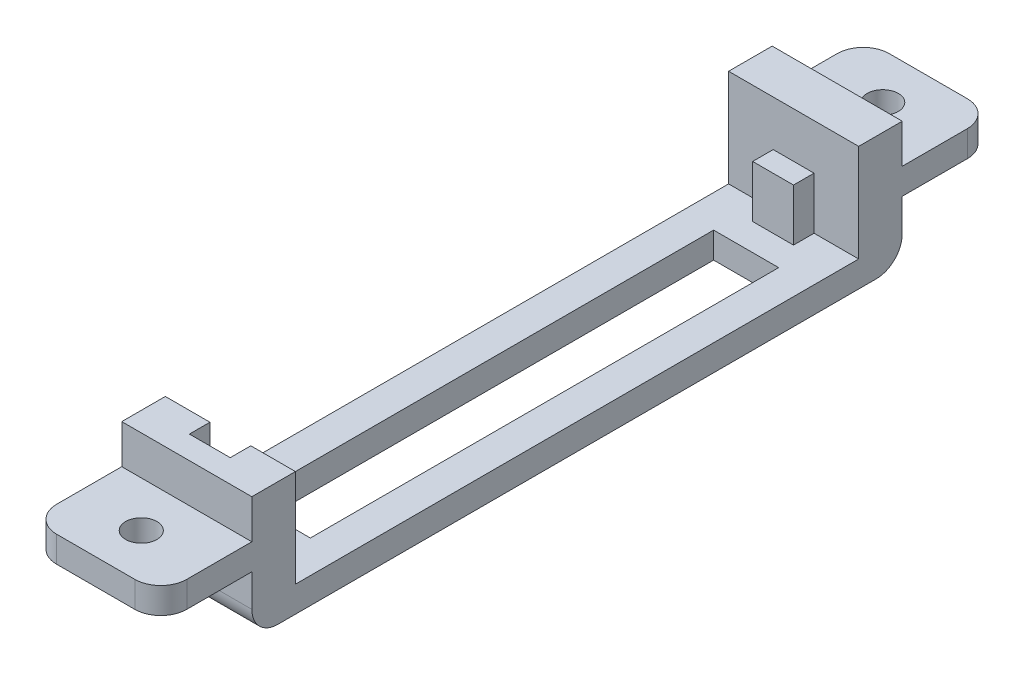
SolidWorks part; units mm, degrees
ref_plane "Front" through (0, 0, 0) normal (0, 0, 1) x (1, 0, 0)
ref_plane "Top" through (0, 0, 0) normal (0, 1, 0) x (1, 0, 0)
ref_plane "Right" through (0, 0, 0) normal (1, 0, 0) x (0, 0, -1)
sketch "Sketch1" plane through (0, 0, 0) normal (0, 1, 0) x (1, 0, 0)
  line L0 (-6.35, 0) -> (6.35, 0) construction
  line L1 (-6.35, -31.75) -> (6.35, -31.75)
  line L2 (-6.35, -31.75) -> (-6.35, 31.75)
  line L3 (-6.35, 31.75) -> (6.35, 31.75)
  line L4 (6.35, -31.75) -> (6.35, 31.75)
  line L5 (-6.35, -31.75) -> (6.35, 31.75) construction
  line L6 (-6.35, 31.75) -> (6.35, -31.75) construction
  line L7 (-3.175, -22.86) -> (3.175, -22.86)
  line L8 (-3.175, -22.86) -> (-3.175, 22.86)
  line L9 (-3.175, 22.86) -> (3.175, 22.86)
  line L10 (3.175, -22.86) -> (3.175, 22.86)
  line L11 (-3.175, -22.86) -> (3.175, 22.86) construction
  line L12 (-3.175, 22.86) -> (3.175, -22.86) construction
  line L13 (0, 31.75) -> (0, -31.75) construction
  point P0 (0, 0)
  point P6 (0, 0)
  dimension "D1" = 63.5
  dimension "D2" = 12.7
  dimension "D3" = 6.35
  dimension "D4" = 45.72
extrude "Boss-Extrude1" add sketch "Sketch1" along normal blind 2.54
sketch "Sketch2" plane through (0, 2.54, 0) normal (0, 1, 0) x (1, 0, 0)
  line L0 (-6.35, 31.75) -> (6.35, 31.75)
  line L1 (-6.35, 31.75) -> (-6.35, -31.75) construction
  line L2 (6.35, -31.75) -> (6.35, 31.75) construction
  line L3 (6.35, 31.75) -> (6.35, 27.4955)
  line L4 (6.35, 27.4955) -> (1.9939, 27.4955)
  line L5 (1.9939, 27.4955) -> (1.9939, 25.4889)
  line L6 (1.9939, 25.4889) -> (-1.9939, 25.4889)
  line L7 (-1.9939, 25.4889) -> (-1.9939, 27.4955)
  line L8 (-1.9939, 27.4955) -> (-6.35, 27.4955)
  line L9 (-6.35, 27.4955) -> (-6.35, 31.75)
  line L10 (-6.35, -27.4955) -> (-6.35, -31.75)
  line L11 (-6.35, -31.75) -> (6.35, -31.75)
  line L12 (6.35, -31.75) -> (6.35, -27.4955)
  line L13 (6.35, -27.4955) -> (1.9939, -27.4955)
  line L14 (1.9939, -27.4955) -> (1.9939, -29.5021)
  line L15 (1.9939, -29.5021) -> (-1.9939, -29.5021)
  line L16 (-1.9939, -29.5021) -> (-1.9939, -27.4955)
  line L17 (-1.9939, -27.4955) -> (-6.35, -27.4955)
  line L18 (0, 31.75) -> (0, -31.75) construction
  line L19 (6.35, 31.75) -> (-6.35, 31.75) construction
  line L20 (-6.35, -31.75) -> (6.35, -31.75) construction
  line L21 (-6.35, 0) -> (6.35, 0) construction
  point P26 (0, -29.5021)
  point P28 (0, 25.4889)
  dimension "D1" = 2.0066
  dimension "D2" = 3.9878
  dimension "D3" = 63.5
  dimension "D4" = 54.991
extrude "Boss-Extrude2" add sketch "Sketch2" along normal blind 9.525
sketch "Sketch5" plane through (0, 12.065, 0) normal (0, 1, 0) x (1, 0, 0)
  line L1 (-1.9939, 25.4889) -> (1.9939, 25.4889)
  line L2 (-1.9939, 25.4889) -> (-1.9939, 27.4955)
  line L3 (-1.9939, 27.4955) -> (1.9939, 27.4955)
  line L4 (1.9939, 25.4889) -> (1.9939, 27.4955)
extrude "Cut-Extrude1" cut sketch "Sketch5" against normal blind 4.445
ref_plane "Plane1" through (0, 8.255, 0) normal (0, 1, 0) x (1, 0, 0)
sketch "Sketch7" plane through (0, 8.255, 0) normal (0, 1, 0) x (1, 0, 0)
  line L0 (6.35, 31.75) -> (-6.35, 31.75) construction
  line L1 (6.35, 31.75) -> (-6.35, 31.75)
  line L2 (-6.35, 31.75) -> (-6.35, 40.64)
  line L3 (-6.35, 40.64) -> (6.35, 40.64)
  line L4 (6.35, 40.64) -> (6.35, 31.75)
  line L5 (-6.35, 40.64) -> (6.35, 31.75) construction
  line L6 (-6.35, 31.75) -> (6.35, 40.64) construction
  line L7 (-6.35, 0) -> (6.35, 0) construction
  line L8 (-6.35, 27.4955) -> (-6.35, -27.4955) construction
  line L9 (6.35, -27.4955) -> (6.35, 27.4955) construction
  line L10 (-6.35, -31.75) -> (6.35, -40.64) construction
  line L11 (-6.35, -40.64) -> (6.35, -31.75) construction
  line L12 (6.35, -40.64) -> (6.35, -31.75)
  line L13 (-6.35, -40.64) -> (6.35, -40.64)
  line L14 (-6.35, -31.75) -> (-6.35, -40.64)
  line L15 (6.35, -31.75) -> (-6.35, -31.75)
  circle A0 centre (0, 36.195) radius 1.524
  circle A1 centre (0, -36.195) radius 1.524
  dimension "D1" = 3.048
  dimension "D2" = 72.39
extrude "Boss-Extrude4" add sketch "Sketch7" against normal blind 2.54
fillet "Fillet1" radius 2.54 6 edges at (6.35, 6.985, -40.64) (-6.35, 6.985, -40.64) (0, 0, -31.75) (0, 0, 31.75) (6.35, 6.985, 40.64) (-6.35, 6.985, 40.64)
